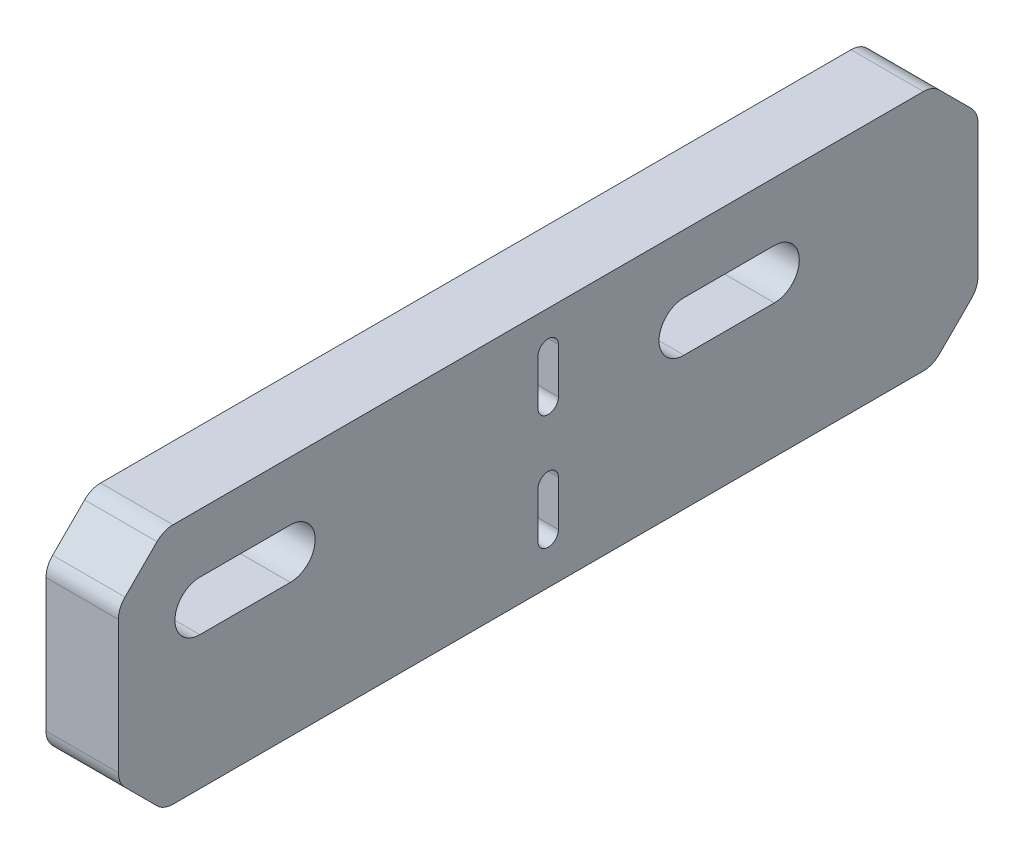
SolidWorks part; units mm, degrees
ref_plane "Front Plane" through (0, 0, 0) normal (0, 0, 1) x (1, 0, 0)
ref_plane "Top Plane" through (0, 0, 0) normal (0, 1, 0) x (1, 0, 0)
ref_plane "Right Plane" through (0, 0, 0) normal (1, 0, 0) x (0, 0, -1)
sketch "Sketch1" plane through (0, 0, 0) normal (1, 0, 0) x (0, 0, -1)
  line L0 (-6.35, -2.025) -> (6.35, -2.025) construction
  line L1 (-40, 10.875) -> (40, 10.875)
  line L2 (-40, 10.875) -> (-40, -10.875)
  line L3 (-40, -10.875) -> (40, -10.875)
  line L4 (40, 10.875) -> (40, -10.875)
  line L5 (-40, 10.875) -> (40, -10.875) construction
  line L6 (-40, -10.875) -> (40, 10.875) construction
  line L7 (0, 4.325) -> (0, -8.375) construction
  point P0 (0, 0)
  point P6 (-33.5, 1.625)
  point P7 (20, 1.625)
  point P8 (-6.35, -2.025)
  point P9 (6.35, -2.025)
  point P12 (0, -2.025)
  point P13 (0, 4.325)
  point P14 (0, -8.375)
  dimension "D1" = 21.75
  dimension "D2" = 6.5
  dimension "D3" = 9.25
  dimension "D4" = 80
  dimension "D5" = 12.9
  dimension "D7" = 12.7
  dimension "D8" = 12.7
  dimension "D9" = 53.5
extrude "Main" add sketch "Sketch1" along normal blind 8
hole_wizard "M5 Clearance Hole1" positions "Sketch3" profile "Sketch2" hole size "M5" standard "ANSI Metric" end condition through all
sketch "Sketch3" plane through (0, 0, 0) normal (-1, 0, 0) x (0, 0, 1)
  point P0 (-20, 1.625)
  point P3 (33.5, 1.625)
sketch "Sketch2" plane through (0, 1.625, -20) normal (0, 1, 0) x (0, 0, 1)
  line L0 (0, 0) -> (0, 8)
  line L1 (0, 8) -> (2.75, 8)
  line L2 (2.75, 8) -> (2.75, 0)
  line L5 (2.75, 0) -> (0, 0)
  line L11 (0, -6.35) -> (0, 107.95) construction
  dimension "Thru Hole Dia." = 5.5
  dimension "Thru Hole Depth" = 8
hole_wizard "#2 Clearance Hole1" positions "Sketch8" profile "Sketch7" hole size "#2" standard "ANSI Inch" end condition through all
sketch "Sketch8" plane through (0, 0, 0) normal (-1, 0, 0) x (0, 0, 1)
  point P7 (0, -8.375)
  point P9 (0, 4.325)
sketch "Sketch7" plane through (0, -8.375, 0) normal (0, 1, 0) x (0, 0, 1)
  line L0 (0, 0) -> (0, 8)
  line L1 (0, 8) -> (1.1303, 8)
  line L2 (1.1303, 8) -> (1.1303, 0)
  line L5 (1.1303, 0) -> (0, 0)
  line L11 (0, -6.35) -> (0, 107.95) construction
  dimension "Thru Hole Dia." = 2.2606
  dimension "Thru Hole Depth" = 8
sketch "Sketch9" plane through (8, 0, 0) normal (1, 0, 0) x (0, 0, -1)
  line L0 (-6.35, -2.025) -> (6.35, -2.025) construction
  line L1 (-10.35, -6.025) -> (10.35, -6.025)
  line L2 (-10.35, -6.025) -> (-10.35, 1.975)
  line L3 (-10.35, 1.975) -> (10.35, 1.975)
  line L4 (10.35, -6.025) -> (10.35, 1.975)
  line L5 (-10.35, -6.025) -> (10.35, 1.975) construction
  line L6 (-10.35, 1.975) -> (10.35, -6.025) construction
  point P0 (0, -2.025)
  dimension "D1" = 4
  dimension "D2" = 4
sketch "Sketch13" plane through (0, 0, 0) normal (-1, 0, 0) x (0, 0, 1)
  line L0 (40, 10.875) -> (47.5, 10.875)
  line L1 (47.5, 10.875) -> (47.5, -15.875)
  line L2 (47.5, -15.875) -> (-47.5, -15.875)
  line L3 (-47.5, -15.875) -> (-47.5, 10.875)
  line L4 (-40, 10.875) -> (-40, -10.875)
  line L5 (-40, -10.875) -> (40, -10.875)
  line L6 (40, -10.875) -> (40, 10.875)
  line L7 (40, 10.875) -> (-40, 10.875)
  line L8 (-40, 10.875) -> (-40, -10.875)
  line L9 (-40, -10.875) -> (40, -10.875)
  line L10 (40, -10.875) -> (40, 10.875)
  line L12 (-47.5, 10.875) -> (-40, 10.875)
  dimension "D2" = 7.5
  dimension "D3" = 5
  dimension "D1" = 0
extrude "Spacer" add sketch "Sketch13" against normal up to vertex (8 mm away) up to point (8, -10.875, 40)
sketch "Sketch14" plane through (0, 0, 0) normal (-1, 0, 0) x (0, 0, 1)
  line L0 (38.5, 1.625) -> (28.5, 1.625) construction
  line L1 (38.5, -1.125) -> (28.5, -1.125)
  line L2 (38.5, 4.375) -> (28.5, 4.375)
  line L3 (-15, 1.625) -> (-25, 1.625) construction
  line L4 (-15, -1.125) -> (-25, -1.125)
  line L5 (-15, 4.375) -> (-25, 4.375)
  line L6 (0, -5.875) -> (0, -10.875) construction
  line L7 (1.1303, -5.875) -> (1.1303, -10.875)
  line L8 (-1.1303, -5.875) -> (-1.1303, -10.875)
  line L9 (0, 6.825) -> (0, 1.825) construction
  line L10 (1.1303, 6.825) -> (1.1303, 1.825)
  line L11 (-1.1303, 6.825) -> (-1.1303, 1.825)
  arc A0 (38.5, -1.125) -> (38.5, 4.375) centre (38.5, 1.625) ccw
  arc A1 (28.5, 4.375) -> (28.5, -1.125) centre (28.5, 1.625) ccw
  arc A2 (-15, -1.125) -> (-15, 4.375) centre (-15, 1.625) ccw
  arc A3 (-25, 4.375) -> (-25, -1.125) centre (-25, 1.625) ccw
  arc A4 (1.1303, -5.875) -> (-1.1303, -5.875) centre (0, -5.875) ccw
  arc A5 (-1.1303, -10.875) -> (1.1303, -10.875) centre (0, -10.875) ccw
  arc A6 (1.1303, 6.825) -> (-1.1303, 6.825) centre (0, 6.825) ccw
  arc A7 (-1.1303, 1.825) -> (1.1303, 1.825) centre (0, 1.825) ccw
  circle A8 centre (0, -8.375) radius 1.1303 construction
  circle A9 centre (33.5, 1.625) radius 2.75 construction
  point P2 (33.5, 1.625)
  point P9 (-20, 1.625)
  point P17 (0, -8.375)
  point P26 (0, 4.325)
  dimension "D1" = 5
  dimension "D2" = 10
extrude "Cut-Extrude3" cut sketch "Sketch14" against normal blind 10
sketch "Sketch10" plane through (0, 0, 0) normal (-1, 0, 0) x (0, 0, 1)
  circle A0 centre (0, -2.025) radius 2.75
  dimension "D1" = 5.5
extrude "Cut-Extrude1" [suppressed] cut sketch "Sketch10" against normal through all
sketch "Sketch12" plane through (8, 0, 0) normal (1, 0, 0) x (0, 0, -1)
  line L0 (-41, 5.125) -> (-26, 5.125) construction
  line L1 (-41, 7.875) -> (-26, 7.875)
  line L2 (-41, 2.375) -> (-26, 2.375)
  line L3 (12.5, 5.125) -> (27.5, 5.125) construction
  line L4 (12.5, 7.875) -> (27.5, 7.875)
  line L5 (12.5, 2.375) -> (27.5, 2.375)
  line L6 (-7.5, 5.375) -> (7.5, 5.375) construction
  line L7 (-7.5, 6.5053) -> (7.5, 6.5053)
  line L8 (-7.5, 4.2447) -> (7.5, 4.2447)
  line L9 (-7.5, -7.325) -> (7.5, -7.325) construction
  line L10 (-7.5, -6.1947) -> (7.5, -6.1947)
  line L11 (-7.5, -8.4553) -> (7.5, -8.4553)
  arc A0 (-41, 7.875) -> (-41, 2.375) centre (-41, 5.125) ccw
  arc A1 (-26, 2.375) -> (-26, 7.875) centre (-26, 5.125) ccw
  arc A2 (12.5, 7.875) -> (12.5, 2.375) centre (12.5, 5.125) ccw
  arc A3 (27.5, 2.375) -> (27.5, 7.875) centre (27.5, 5.125) ccw
  arc A4 (-7.5, 6.5053) -> (-7.5, 4.2447) centre (-7.5, 5.375) ccw
  arc A5 (7.5, 4.2447) -> (7.5, 6.5053) centre (7.5, 5.375) ccw
  arc A6 (-7.5, -6.1947) -> (-7.5, -8.4553) centre (-7.5, -7.325) ccw
  arc A7 (7.5, -8.4553) -> (7.5, -6.1947) centre (7.5, -7.325) ccw
  circle A8 centre (-33.5, 5.125) radius 2.75 construction
  circle A9 centre (0, 5.375) radius 1.1303 construction
  point P2 (-33.5, 5.125)
  point P9 (20, 5.125)
  point P17 (0, 5.375)
  point P25 (0, -7.325)
  dimension "D1" = 15
  dimension "D2" = 15
extrude "Cut-Extrude2" [suppressed] cut sketch "Sketch12" against normal blind 10
chamfer "Chamfer1" distance 5 angle 45 4 edges at (4, 10.875, -47.5) (4, -15.875, -47.5) (4, 10.875, 47.5) (4, -15.875, 47.5)
fillet "Fillet1" radius 2.5 8 edges at (4, -15.875, -42.5) (4, -10.875, -47.5) (4, 5.875, -47.5) (4, 10.875, -42.5) (4, 10.875, 42.5) (4, 5.875, 47.5) (4, -10.875, 47.5) (4, -15.875, 42.5)
